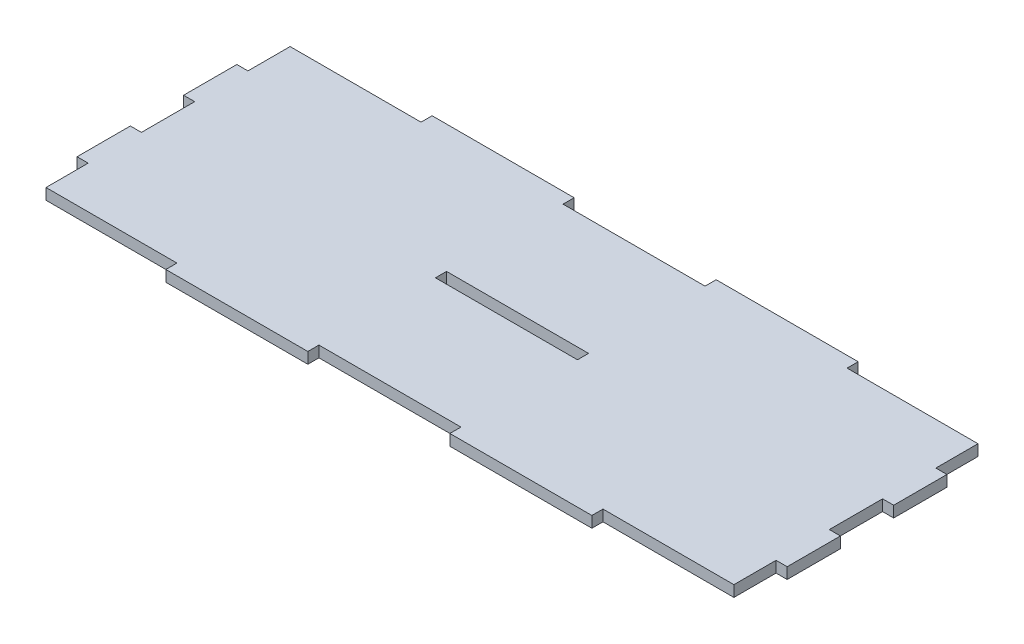
SolidWorks part; units mm, degrees
ref_plane "Front Plane" through (0, 0, 0) normal (0, 0, 1) x (1, 0, 0)
ref_plane "Top Plane" through (0, 0, 0) normal (0, 1, 0) x (1, 0, 0)
ref_plane "Right Plane" through (0, 0, 0) normal (1, 0, 0) x (0, 0, -1)
sketch "Sketch1" plane through (0, 0, 0) normal (0, 1, 0) x (1, 0, 0)
  line L1 (-101.6, -38.1) -> (101.6, -38.1)
  line L2 (-101.6, -38.1) -> (-101.6, 38.1)
  line L3 (-101.6, 38.1) -> (101.6, 38.1)
  line L4 (101.6, -38.1) -> (101.6, 38.1)
  line L5 (-101.6, -38.1) -> (101.6, 38.1) construction
  line L6 (-101.6, 38.1) -> (101.6, -38.1) construction
  point P0 (0, 0)
  dimension "D1" = 203.2
  dimension "D2" = 76.2
extrude "Boss-Extrude1" add sketch "Sketch1" along normal blind 3.175
sketch "Sketch2" plane through (0, 3.175, 0) normal (0, 1, 0) x (1, 0, 0)
  line L1 (-101.6, 38.1) -> (-60.96, 38.1)
  line L2 (-101.6, 38.1) -> (-101.6, 34.925)
  line L3 (-101.6, 34.925) -> (-60.96, 34.925)
  line L4 (-60.96, 38.1) -> (-60.96, 34.925)
  line L5 (-101.6, -38.1) -> (-60.96, -38.1)
  line L6 (-101.6, -38.1) -> (-101.6, -34.925)
  line L7 (-101.6, -34.925) -> (-60.96, -34.925)
  line L8 (-60.96, -38.1) -> (-60.96, -34.925)
  dimension "D1" = 40.64
  dimension "D2" = 3.175
  dimension "D3" = 3.175
extrude "Cut-Extrude1" cut sketch "Sketch2" against normal blind 3.175
pattern_linear "LPattern1" count 3 spacing 81.28 along (1, 0, 0) of "Cut-Extrude1"
sketch "Sketch3" plane through (0, 3.175, 0) normal (0, 1, 0) x (1, 0, 0)
  line L0 (-42.8539, 38.1) -> (80.0805, 38.1) construction
  line L2 (-56.9221, -38.1) -> (40.64, -38.1) construction
  line L3 (98.425, 38.1) -> (101.6, 38.1)
  line L4 (98.425, 38.1) -> (98.425, 22.86)
  line L5 (-101.6, 22.4009) -> (-101.6, -18.5051) construction
  line L6 (98.425, 22.86) -> (101.6, 22.86)
  line L7 (101.6, 22.8338) -> (101.6, -4.2205) construction
  line L8 (101.6, 38.1) -> (101.6, 22.86)
  line L10 (-98.425, 38.1) -> (-101.6, 38.1)
  line L11 (-98.425, 38.1) -> (-98.425, 22.86)
  line L12 (-98.425, 22.86) -> (-101.6, 22.86)
  line L13 (-101.6, 38.1) -> (-101.6, 22.86)
  dimension "D1" = 3.175
  dimension "D2" = 15.24
  dimension "D3" = 3.175
extrude "Cut-Extrude2" cut sketch "Sketch3" against normal blind 3.175
pattern_linear "LPattern2" count 3 spacing 30.48 along (0, 0, 1) of "Cut-Extrude2"
sketch "Sketch4" plane through (0, 3.175, 0) normal (0, 1, 0) x (1, 0, 0)
  line L1 (-20.32, -1.5875) -> (20.32, -1.5875)
  line L2 (-20.32, -1.5875) -> (-20.32, 1.5875)
  line L3 (-20.32, 1.5875) -> (20.32, 1.5875)
  line L4 (20.32, -1.5875) -> (20.32, 1.5875)
  line L5 (-20.32, -1.5875) -> (20.32, 1.5875) construction
  line L6 (-20.32, 1.5875) -> (20.32, -1.5875) construction
  point P0 (0, 0)
  dimension "D1" = 3.175
  dimension "D2" = 40.64
extrude "Cut-Extrude3" cut sketch "Sketch4" against normal blind 3.175
